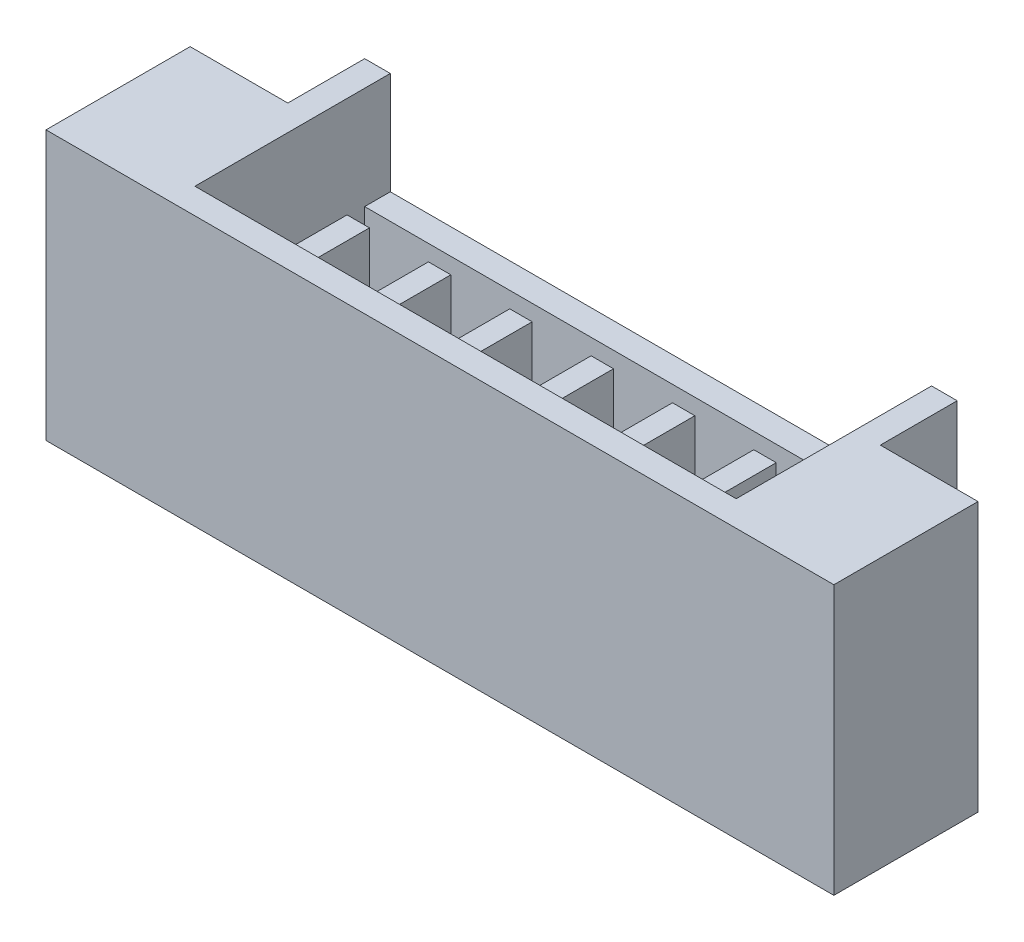
SolidWorks part; units mm, degrees
ref_plane "Front Plane" through (0, 0, 0) normal (0, 0, 1) x (1, 0, 0)
ref_plane "Top Plane" through (0, 0, 0) normal (0, 1, 0) x (1, 0, 0)
ref_plane "Right Plane" through (0, 0, 0) normal (1, 0, 0) x (0, 0, -1)
sketch "Sketch1" plane through (0, 0, 0) normal (0, 1, 0) x (1, 0, 0)
  line L0 (0, 1.725) -> (0, -1.725) construction
  line L1 (-6.15, 1.725) -> (6.15, 1.725)
  line L2 (-6.15, 1.725) -> (-6.15, -1.725)
  line L3 (-6.15, -1.725) -> (6.15, -1.725)
  line L4 (6.15, 1.725) -> (6.15, -1.725)
  line L5 (-6.15, 1.725) -> (6.15, -1.725) construction
  line L6 (-6.15, -1.725) -> (6.15, 1.725) construction
  line L8 (-6.15, -1.725) -> (6.15, -1.725)
  line L9 (-6.15, -1.725) -> (-6.15, 0.525)
  line L10 (-6.15, 0.525) -> (6.15, 0.525)
  line L11 (6.15, -1.725) -> (6.15, 0.525)
  line L12 (-6.15, -1.725) -> (6.15, 0.525) construction
  line L13 (-6.15, 0.525) -> (6.15, -1.725) construction
  line L14 (-4.625, -1.725) -> (4.625, -1.725)
  line L15 (-4.625, -1.725) -> (-4.625, 1.725)
  line L16 (-4.625, 1.725) -> (4.625, 1.725)
  line L17 (4.625, -1.725) -> (4.625, 1.725)
  line L18 (-4.625, -1.725) -> (4.625, 1.725) construction
  line L19 (-4.625, 1.725) -> (4.625, -1.725) construction
  point P0 (0, 0)
  point P8 (0, -0.6)
  point P13 (0, 0)
  dimension "D1" = 12.3
  dimension "D2" = 3.45
  dimension "D3" = 2.25
  dimension "D4" = 9.25
extrude "Boss-Extrude1" add sketch "Sketch1" along normal blind 4.2 contours L3 L15 L10 L2 | L10 L17 L1 L15 | L8 L17 L10 L15 | L17 L3 L4 L10
sketch "Sketch2" plane through (0, 4.2, 0) normal (0, 1, 0) x (1, 0, 0)
  line L0 (-4.625, 1.725) -> (4.625, 1.725) construction
  line L1 (4.225, -1.325) -> (-4.225, -1.325)
  line L2 (4.225, -1.325) -> (4.225, 1.325)
  line L3 (4.225, 1.325) -> (-4.225, 1.325)
  line L4 (-4.225, -1.325) -> (-4.225, 1.325)
  line L5 (4.225, -1.325) -> (-4.225, 1.325) construction
  line L6 (4.225, 1.325) -> (-4.225, -1.325) construction
  line L7 (-4.225, 1.325) -> (-4.225, 1.725) construction
  line L8 (-4.225, 1.325) -> (-4.625, 1.325) construction
  line L9 (-4.625, 0.525) -> (-4.625, 1.725) construction
  point P0 (0, 0)
  dimension "D1" = 0.4
extrude "Cut-Extrude1" cut sketch "Sketch2" against normal offset from surface (3.2 mm away) 1 up to face at (0, 0, -0.2625)
sketch "Sketch3" plane through (0, 4.2, 0) normal (0, 1, 0) x (1, 0, 0)
  line L0 (-4.625, 1.725) -> (4.625, 1.725) construction
  line L1 (-4.225, 1.325) -> (4.225, 1.325)
  line L2 (-4.225, 1.325) -> (-4.225, 1.725)
  line L3 (-4.225, 1.725) -> (4.225, 1.725)
  line L4 (4.225, 1.325) -> (4.225, 1.725)
  line L5 (4.225, -1.325) -> (4.225, 1.325) construction
extrude "Cut-Extrude2" cut sketch "Sketch3" against normal offset from surface (1.6 mm away) 2.6 up to face at (0, 0, -0.2625)
sketch "Sketch4" plane through (0, 1, 0) normal (0, 1, 0) x (1, 0, 0)
  line L0 (-4.225, -0.325) -> (4.225, -0.325) construction
  line L1 (-4.225, 1.725) -> (-4.225, -1.325) construction
  line L2 (4.225, -1.325) -> (4.225, 1.725) construction
  line L3 (4.225, -1.325) -> (-4.225, -1.325) construction
  line L4 (0, 1.325) -> (0, -1.325) construction
  line L5 (-4.225, 1.325) -> (4.225, 1.325) construction
  line L6 (0.46, 0.175) -> (0.46, -0.825)
  line L7 (-0.81, 0.175) -> (-0.46, 0.175)
  line L8 (-0.81, 0.175) -> (-0.81, -0.825)
  line L9 (-0.81, -0.825) -> (-0.46, -0.825)
  line L10 (-0.46, 0.175) -> (-0.46, -0.825)
  line L11 (-0.81, 0.175) -> (-0.46, -0.825) construction
  line L12 (-0.81, -0.825) -> (-0.46, 0.175) construction
  line L13 (0.46, -0.825) -> (0.81, -0.825)
  line L14 (0.81, 0.175) -> (0.81, -0.825)
  line L15 (0.46, 0.175) -> (0.81, 0.175)
  line L16 (1.73, 0.175) -> (1.73, -0.825)
  line L17 (1.73, -0.825) -> (2.08, -0.825)
  line L18 (2.08, 0.175) -> (2.08, -0.825)
  line L19 (1.73, 0.175) -> (2.08, 0.175)
  line L20 (3, 0.175) -> (3, -0.825)
  line L21 (3, -0.825) -> (3.35, -0.825)
  line L22 (3.35, 0.175) -> (3.35, -0.825)
  line L23 (3, 0.175) -> (3.35, 0.175)
  line L24 (-3, 0.175) -> (-3.35, 0.175)
  line L25 (-3.35, 0.175) -> (-3.35, -0.825)
  line L26 (-3, -0.825) -> (-3.35, -0.825)
  line L27 (-3, 0.175) -> (-3, -0.825)
  line L28 (-1.73, 0.175) -> (-2.08, 0.175)
  line L29 (-2.08, 0.175) -> (-2.08, -0.825)
  line L30 (-1.73, -0.825) -> (-2.08, -0.825)
  line L31 (-1.73, 0.175) -> (-1.73, -0.825)
  point P12 (-0.635, -0.325)
  dimension "D1" = 1
  dimension "D2" = 0.35
  dimension "D3" = 1
  dimension "D4" = 1.27
  dimension "D5" = 4
extrude "Boss-Extrude2" add sketch "Sketch4" along normal offset from surface (2.5 mm away) 0.7 up to face at (0, 4.2, -0.2417)
